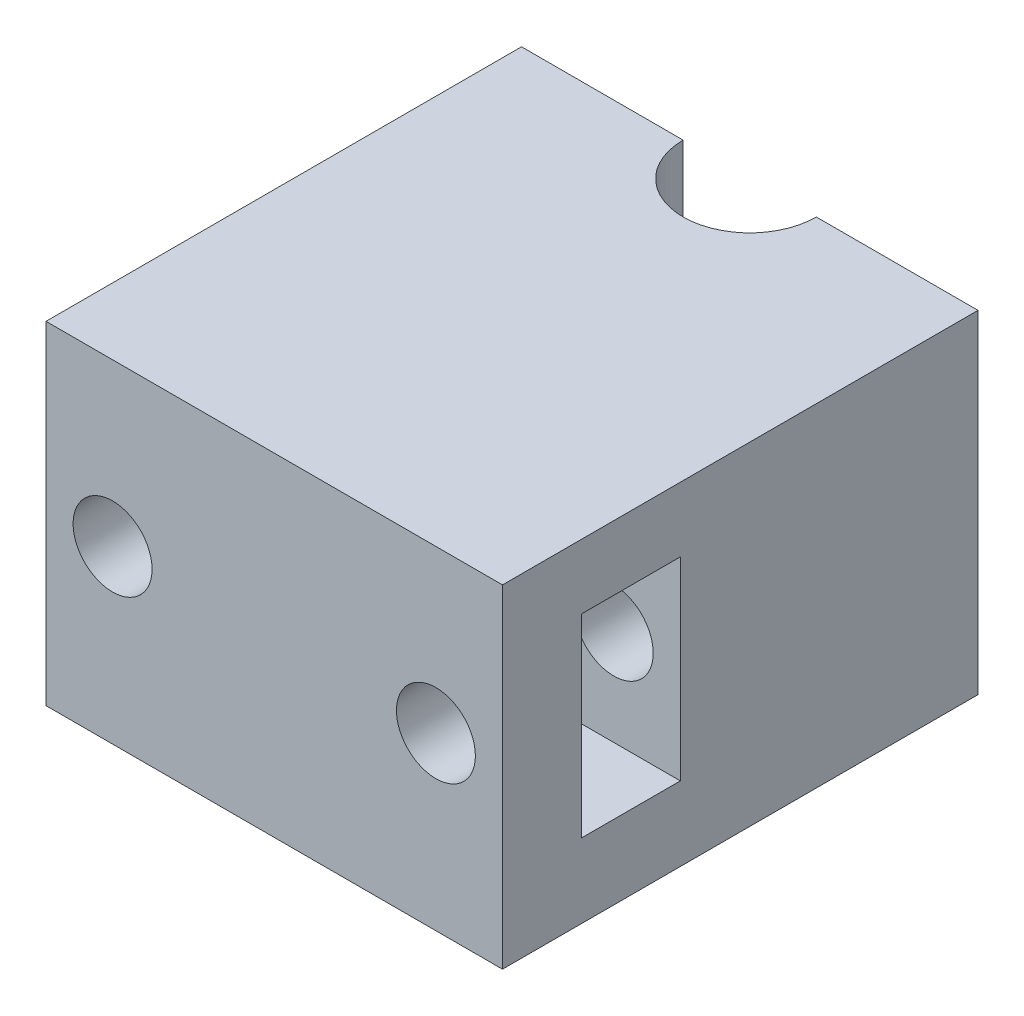
SolidWorks part; units mm, degrees
ref_plane "Спереди" through (0, 0, 0) normal (0, 0, 1) x (1, 0, 0)
ref_plane "Сверху" through (0, 0, 0) normal (0, 1, 0) x (1, 0, 0)
ref_plane "Справа" through (0, 0, 0) normal (1, 0, 0) x (0, 0, -1)
sketch "Sketch1" plane through (0, 0, 0) normal (0, 1, 0) x (1, 0, 0)
  line L1 (24, -25) -> (-24, -25)
  line L2 (24, -25) -> (24, 25)
  line L3 (24, 25) -> (-24, 25)
  line L4 (-24, -25) -> (-24, 25)
  line L5 (24, -25) -> (-24, 25) construction
  line L6 (24, 25) -> (-24, -25) construction
  point P0 (0, 0)
  dimension "D1" = 48
  dimension "D2" = 50
extrude "Boss-Extrude1" add sketch "Sketch1" along normal blind 70
sketch "Sketch2" plane through (24, 0, 0) normal (1, 0, 0) x (0, 0, -1)
  line L0 (-25, 35) -> (25, 35) construction
  line L1 (-25, 70) -> (-25, 0) construction
  line L2 (25, 70) -> (25, 0) construction
  line L3 (-11.5, 35) -> (-11.5, 70) construction
  line L4 (-16.7, 24.8) -> (-6.3, 24.8) construction
  line L5 (-16.7, 24.8) -> (-16.7, 45.2) construction
  line L6 (-16.7, 45.2) -> (-6.3, 45.2) construction
  line L7 (-6.3, 24.8) -> (-6.3, 45.2) construction
  line L8 (-16.7, 24.8) -> (-6.3, 45.2) construction
  line L9 (-16.7, 45.2) -> (-6.3, 24.8) construction
  line L10 (-25, 70) -> (25, 70) construction
  line L11 (-11.5, 35) -> (-11.5, 0) construction
  line L12 (-25, 0) -> (25, 0) construction
  line L13 (-5.7606, 42.8) -> (-5.7606, 27.2) construction
  line L14 (-6.3, 42.8) -> (-16.7, 42.8)
  line L15 (-6.3, 42.8) -> (-6.3, 63.2)
  line L16 (-6.3, 63.2) -> (-16.7, 63.2)
  line L17 (-16.7, 42.8) -> (-16.7, 63.2)
  line L18 (-6.3, 42.8) -> (-16.7, 63.2) construction
  line L19 (-6.3, 63.2) -> (-16.7, 42.8) construction
  line L20 (-6.3, 6.8) -> (-16.7, 6.8)
  line L21 (-6.3, 6.8) -> (-6.3, 27.2)
  line L22 (-6.3, 27.2) -> (-16.7, 27.2)
  line L23 (-16.7, 6.8) -> (-16.7, 27.2)
  line L24 (-6.3, 6.8) -> (-16.7, 27.2) construction
  line L25 (-6.3, 27.2) -> (-16.7, 6.8) construction
  line L26 (-16.7, 53) -> (-25, 53) construction
  line L27 (-16.7, 17) -> (-25, 17) construction
  point P6 (-11.5, 35)
  point P15 (-11.5, 53)
  point P23 (-11.5, 17)
  point P30 (-5.7606, 35)
  dimension "D1" = 10.4
  dimension "D2" = 20.4
  dimension "D3" = 13.5
  dimension "D5" = 7.8
extrude "Cut-Extrude1" cut sketch "Sketch2" against normal offset from surface (45 mm away) 3 up to face at (-24, 35, 0)
sketch "Sketch3" plane through (0, 0, 25) normal (0, 0, 1) x (1, 0, 0)
  line L0 (-24, 35) -> (24, 35) construction
  line L1 (-24, 70) -> (-24, 0) construction
  line L2 (24, 70) -> (24, 0) construction
  line L3 (17, 17) -> (17, 53) construction
  line L4 (-17, 17) -> (-17, 53) construction
  line L5 (24, 53) -> (-24, 53) construction
  line L6 (24, 17) -> (-24, 17) construction
  circle A0 centre (-17, 35) radius 4.15 construction
  circle A1 centre (17, 35) radius 4.15 construction
  circle A2 centre (17, 53) radius 4.15
  circle A3 centre (-17, 53) radius 4.15
  circle A4 centre (-17, 17) radius 4.15
  circle A5 centre (17, 17) radius 4.15
  point P10 (0, 35)
  point P13 (17, 35)
  point P17 (-17, 35)
  dimension "D1" = 34
  dimension "D2" = 8.3
  dimension "D3" = 17
extrude "Cut-Extrude2" cut sketch "Sketch3" against normal through all
sketch "Sketch4" plane through (0, 70, 0) normal (0, 1, 0) x (1, 0, 0)
  line L0 (0, 25) -> (0, -25) construction
  line L1 (24, 25) -> (-24, 25) construction
  line L2 (-24, -25) -> (24, -25) construction
  arc A0 (-7, 25) -> (7, 25) centre (0, 25) ccw
  dimension "D1" = 7
extrude "Cut-Extrude3" cut sketch "Sketch4" against normal through all and the other way through all
sketch "Sketch5" plane through (0, 0, 0) normal (0, -1, 0) x (1, 0, 0)
  line L1 (-24, -25) -> (24, -25)
  line L2 (-24, -25) -> (-24, 25)
  line L3 (-24, 25) -> (24, 25)
  line L4 (24, -25) -> (24, 25)
  line L5 (-24, -25) -> (24, 25) construction
  line L6 (-24, 25) -> (24, -25) construction
  point P0 (0, 0)
extrude "Cut-Extrude4" cut sketch "Sketch5" against normal up to vertex (35 mm away) up to point (24, 35, 25)
